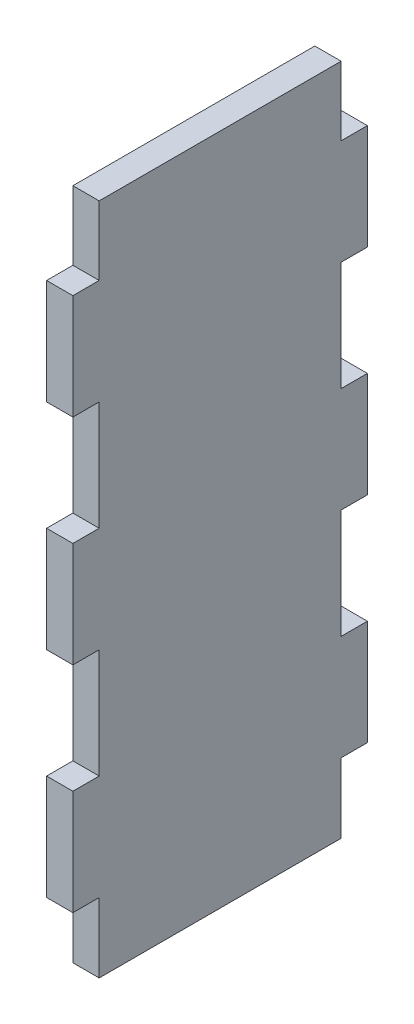
SolidWorks part; units mm, degrees
ref_plane "Front Plane" through (0, 0, 0) normal (0, 0, 1) x (1, 0, 0)
ref_plane "Top Plane" through (0, 0, 0) normal (0, 1, 0) x (1, 0, 0)
ref_plane "Right Plane" through (0, 0, 0) normal (1, 0, 0) x (0, 0, -1)
sketch "Sketch1" plane through (0, 0, 0) normal (1, 0, 0) x (0, 0, -1)
  line L0 (0, 0) -> (0, 50) construction
  line L1 (0, 0) -> (44.1138, 0) construction
  line L3 (-17.78, 45.466) -> (17.78, 45.466)
  line L4 (-17.78, 45.466) -> (-17.78, -45.466)
  line L5 (-17.78, -45.466) -> (17.78, -45.466)
  line L6 (17.78, 45.466) -> (17.78, -45.466)
  dimension "D1" = 90.932
  dimension "D2" = 35.56
  dimension "D3" = 17.78
  dimension "D4" = 45.466
extrude "Extrude1" add sketch "Sketch1" along normal blind 3.175
sketch "Sketch2" plane through (3.175, 0, 0) normal (1, 0, 0) x (0, 0, -1)
  line L1 (-17.78, 45.466) -> (-14.605, 45.466)
  line L2 (-17.78, 45.466) -> (-17.78, 32.258)
  line L3 (-17.78, 32.258) -> (-14.605, 32.258)
  line L4 (-14.605, 45.466) -> (-14.605, 32.258)
  line L5 (-17.78, 19.558) -> (-14.605, 19.558)
  line L6 (-17.78, 19.558) -> (-17.78, 6.35)
  line L7 (-17.78, 6.35) -> (-14.605, 6.35)
  line L8 (-14.605, 19.558) -> (-14.605, 6.35)
  line L9 (-17.78, -6.35) -> (-14.605, -6.35)
  line L10 (-17.78, -6.35) -> (-17.78, -19.558)
  line L11 (-17.78, -19.558) -> (-14.605, -19.558)
  line L12 (-14.605, -6.35) -> (-14.605, -19.558)
  line L13 (-17.78, -32.258) -> (-14.605, -32.258)
  line L14 (-17.78, -32.258) -> (-17.78, -45.466)
  line L15 (-17.78, -45.466) -> (-14.605, -45.466)
  line L16 (-14.605, -32.258) -> (-14.605, -45.466)
  line L17 (-17.78, -58.166) -> (-14.605, -58.166)
  line L18 (-17.78, -58.166) -> (-17.78, -71.374)
  line L19 (-17.78, -71.374) -> (-14.605, -71.374)
  line L20 (-14.605, -58.166) -> (-14.605, -71.374)
  line L22 (0, 0) -> (0, 48.3465) construction
  line L23 (14.605, -32.258) -> (14.605, -45.466)
  line L24 (17.78, -45.466) -> (14.605, -45.466)
  line L25 (17.78, -32.258) -> (17.78, -45.466)
  line L26 (17.78, -32.258) -> (14.605, -32.258)
  line L27 (14.605, -6.35) -> (14.605, -19.558)
  line L28 (17.78, -19.558) -> (14.605, -19.558)
  line L29 (17.78, -6.35) -> (17.78, -19.558)
  line L30 (17.78, -6.35) -> (14.605, -6.35)
  line L31 (14.605, 19.558) -> (14.605, 6.35)
  line L32 (17.78, 6.35) -> (14.605, 6.35)
  line L33 (17.78, 19.558) -> (17.78, 6.35)
  line L34 (17.78, 19.558) -> (14.605, 19.558)
  line L35 (14.605, 45.466) -> (14.605, 32.258)
  line L36 (17.78, 32.258) -> (14.605, 32.258)
  line L37 (17.78, 45.466) -> (17.78, 32.258)
  line L38 (17.78, 45.466) -> (14.605, 45.466)
  dimension "D1" = 13.208
  dimension "D2" = 3.175
extrude "Cut-Extrude1" cut sketch "Sketch2" against normal through all
sketch "Sketch3" plane through (0, 0, 14.605) normal (0, 0, 1) x (1, 0, 0)
  line L0 (0, 45.466) -> (3.175, 45.466)
  line L1 (3.175, 45.466) -> (3.175, 40.581)
  line L4 (3.175, 32.258) -> (3.175, 45.466) construction
  line L5 (0, -45.466) -> (0, -40.6737)
  line L6 (3.175, 40.581) -> (0, 40.581)
  line L8 (0, 32.258) -> (0, 45.466) construction
  line L9 (0, 40.581) -> (0, 45.466)
  line L15 (0, -45.466) -> (0, -32.258) construction
  line L17 (0, -40.6737) -> (3.175, -40.6737)
  line L18 (3.175, -45.466) -> (3.175, -32.258) construction
  line L19 (3.175, -40.6737) -> (3.175, -45.466)
  line L20 (3.175, -45.466) -> (0, -45.466)
extrude "Cut-Extrude2" cut sketch "Sketch3" against normal through all
equation "\"D4@Sketch1\" = \"D1@Sketch1\" / 2"
equation "\"D3@Sketch1\"=\"D2@Sketch1\"/2"
